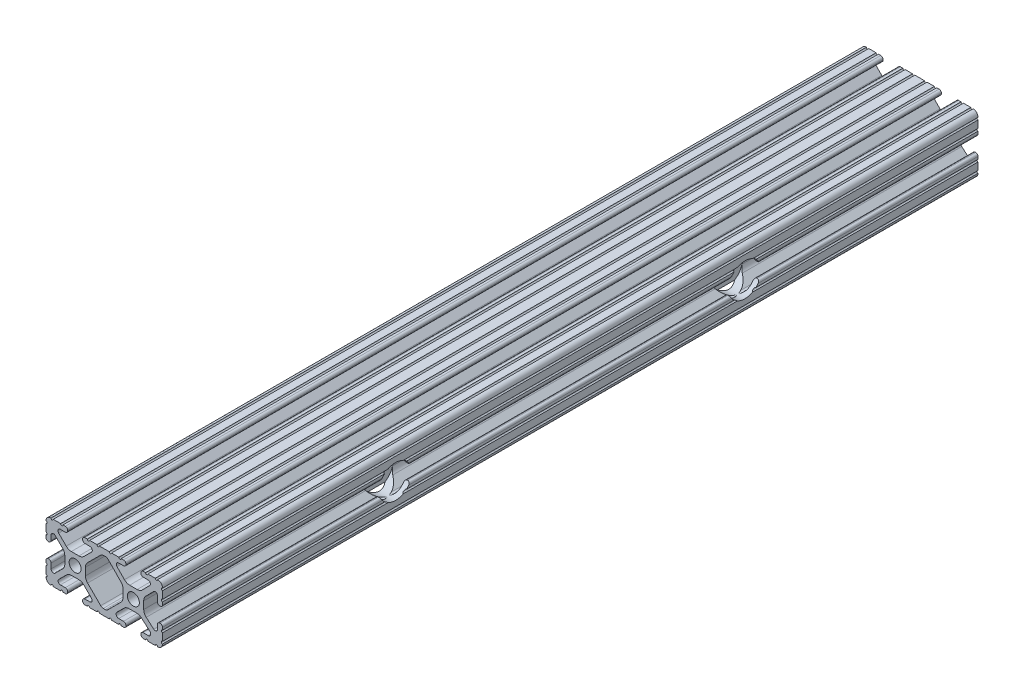
SolidWorks part; units mm, degrees
ref_plane "Front Plane" through (0, 0, 0) normal (0, 0, 1) x (1, 0, 0)
ref_plane "Top Plane" through (0, 0, 0) normal (0, 1, 0) x (1, 0, 0)
ref_plane "Right Plane" through (0, 0, 0) normal (1, 0, 0) x (0, 0, -1)
sketch "Sketch1" plane through (0, 0, 0) normal (0, 0, 1) x (1, 0, 0)
  line L0 (-7.2595, -3.8694) -> (-1.5457, -9.5728)
  line L1 (-8.1915, 1.6223) -> (-8.1915, -1.6223)
  line L2 (-1.504, 9.5765) -> (-7.252, 3.8768)
  line L3 (0.5515, 10.033) -> (-0.3952, 10.033)
  line L4 (7.2829, 3.8459) -> (1.6756, 9.5611)
  line L5 (8.1915, -1.6223) -> (8.1915, 1.6223)
  line L6 (1.5457, -9.5728) -> (7.2595, -3.8694)
  line L7 (-0.4332, -10.033) -> (0.4332, -10.033)
  line L8 (18.0171, 12.7) -> (16.9875, 12.7)
  line L9 (15.9385, 11.651) -> (15.9385, 11.5392)
  line L10 (16.9875, 10.4902) -> (19.1164, 10.4902)
  line L11 (19.8441, 8.7652) -> (16.619, 5.4551)
  line L12 (14.3449, 4.4958) -> (11.0833, 4.4958)
  line L13 (8.817, 5.4472) -> (5.5642, 8.7627)
  line L14 (6.2894, 10.4902) -> (8.4125, 10.4902)
  line L15 (9.4615, 11.5392) -> (9.4615, 11.651)
  line L16 (8.4125, 12.7) -> (7.3829, 12.7)
  line L17 (6.3669, 12.7) -> (3.1496, 12.7)
  line L18 (2.1336, 12.7) -> (-2.1336, 12.7)
  line L19 (-3.1496, 12.7) -> (-6.3669, 12.7)
  line L20 (-7.3829, 12.7) -> (-8.4125, 12.7)
  line L21 (-9.4615, 11.651) -> (-9.4615, 11.5392)
  line L22 (-8.4125, 10.4902) -> (-6.2836, 10.4902)
  line L23 (-5.5326, 8.6661) -> (-8.81, 5.4163)
  line L24 (-11.0455, 4.4958) -> (-14.3545, 4.4958)
  line L25 (-16.59, 5.4163) -> (-19.8674, 8.6661)
  line L26 (-19.1164, 10.4902) -> (-16.9875, 10.4902)
  line L27 (-15.9385, 11.5392) -> (-15.9385, 11.651)
  line L28 (-16.9875, 12.7) -> (-18.0171, 12.7)
  line L29 (-19.0331, 12.7) -> (-22.2504, 12.7)
  line L30 (-25.4, 9.5504) -> (-25.4, 6.3331)
  line L31 (-25.4, 5.3171) -> (-25.4, 4.2375)
  line L32 (-24.401, 3.2385) -> (-24.2392, 3.2385)
  line L33 (-23.1902, 4.2875) -> (-23.1902, 6.3347)
  line L34 (-21.434, 7.0665) -> (-18.148, 3.8082)
  line L35 (-17.2085, 1.5536) -> (-17.2085, -1.6952)
  line L36 (-18.1405, -3.9423) -> (-21.4316, -7.2274)
  line L37 (-23.1902, -6.498) -> (-23.1902, -4.2875)
  line L38 (-24.2392, -3.2385) -> (-24.351, -3.2385)
  line L39 (-25.4, -4.2875) -> (-25.4, -5.3171)
  line L40 (-25.4, -6.3331) -> (-25.4, -9.5504)
  line L41 (-22.2504, -12.7) -> (-19.0331, -12.7)
  line L42 (-18.0171, -12.7) -> (-16.9875, -12.7)
  line L43 (-15.9384, -11.651) -> (-15.9384, -11.5392)
  line L44 (-16.9875, -10.4902) -> (-19.1164, -10.4902)
  line L45 (-19.8341, -8.7551) -> (-16.4966, -5.4237)
  line L46 (-14.2536, -4.4958) -> (-11.1464, -4.4958)
  line L47 (-8.9034, -5.4237) -> (-5.5659, -8.7551)
  line L48 (-6.2836, -10.4902) -> (-8.4125, -10.4902)
  line L49 (-9.4616, -11.5392) -> (-9.4616, -11.651)
  line L50 (-8.4125, -12.7) -> (-7.3829, -12.7)
  line L51 (-6.3669, -12.7) -> (-3.1496, -12.7)
  line L52 (-2.1336, -12.7) -> (2.1336, -12.7)
  line L53 (3.1496, -12.7) -> (6.3669, -12.7)
  line L54 (7.3829, -12.7) -> (8.4125, -12.7)
  line L55 (9.4616, -11.651) -> (9.4616, -11.5392)
  line L56 (8.4125, -10.4902) -> (6.2894, -10.4902)
  line L57 (5.4807, -8.5353) -> (8.5979, -5.4237)
  line L58 (10.8409, -4.4958) -> (14.1026, -4.4958)
  line L59 (16.1879, -5.2766) -> (19.8682, -8.4822)
  line L60 (19.1164, -10.4902) -> (16.9875, -10.4902)
  line L61 (15.9384, -11.5392) -> (15.9384, -11.651)
  line L62 (16.9875, -12.7) -> (18.0171, -12.7)
  line L63 (19.0331, -12.7) -> (22.2504, -12.7)
  line L64 (25.4, -9.5504) -> (25.4, -6.3331)
  line L65 (25.4, -5.3171) -> (25.4, -4.2375)
  line L66 (24.401, -3.2385) -> (24.1892, -3.2385)
  line L67 (23.1902, -4.2375) -> (23.1902, -6.1559)
  line L68 (21.584, -6.8869) -> (18.2982, -4.025)
  line L69 (17.2085, -1.6308) -> (17.2085, 1.6308)
  line L70 (18.1094, 3.8465) -> (21.5263, 7.3534)
  line L71 (23.1902, 6.6769) -> (23.1902, 4.2375)
  line L72 (24.1892, 3.2385) -> (24.401, 3.2385)
  line L73 (25.4, 4.2375) -> (25.4, 5.3171)
  line L74 (25.4, 6.3332) -> (25.4, 9.5504)
  line L75 (22.2504, 12.7) -> (19.0331, 12.7)
  circle A0 centre (-12.7, 0) radius 2.6035
  circle A1 centre (12.7, 0) radius 2.6035
  arc A2 (-1.5457, -9.5728) -> (-0.4332, -10.033) centre (-0.4332, -8.4582) ccw
  arc A3 (-8.1915, -1.6223) -> (-7.2595, -3.8694) centre (-5.0165, -1.6223) ccw
  arc A4 (-7.252, 3.8768) -> (-8.1915, 1.6223) centre (-5.0165, 1.6223) ccw
  arc A5 (-0.3952, 10.033) -> (-1.504, 9.5765) centre (-0.3952, 8.4582) ccw
  arc A6 (1.6756, 9.5611) -> (0.5515, 10.033) centre (0.5515, 8.4582) ccw
  arc A7 (8.1915, 1.6223) -> (7.2829, 3.8459) centre (5.0165, 1.6223) ccw
  arc A8 (7.2595, -3.8694) -> (8.1915, -1.6223) centre (5.0165, -1.6223) ccw
  arc A9 (0.4332, -10.033) -> (1.5457, -9.5728) centre (0.4332, -8.4582) ccw
  arc A10 (18.0171, 12.7) -> (19.0331, 12.7) centre (18.5251, 12.7) ccw
  arc A11 (16.9875, 12.7) -> (15.9385, 11.651) centre (16.9875, 11.651) ccw
  arc A12 (15.9385, 11.5392) -> (16.9875, 10.4902) centre (16.9875, 11.5392) ccw
  arc A13 (19.8441, 8.7652) -> (19.1164, 10.4902) centre (19.1164, 9.4742) ccw
  arc A14 (14.3449, 4.4958) -> (16.619, 5.4551) centre (14.3449, 7.6708) ccw
  arc A15 (8.817, 5.4472) -> (11.0833, 4.4958) centre (11.0833, 7.6708) ccw
  arc A16 (6.2894, 10.4902) -> (5.5642, 8.7627) centre (6.2894, 9.4742) ccw
  arc A17 (8.4125, 10.4902) -> (9.4615, 11.5392) centre (8.4125, 11.5392) ccw
  arc A18 (9.4615, 11.651) -> (8.4125, 12.7) centre (8.4125, 11.651) ccw
  arc A19 (6.3669, 12.7) -> (7.3829, 12.7) centre (6.8749, 12.7) ccw
  arc A20 (2.1336, 12.7) -> (3.1496, 12.7) centre (2.6416, 12.7) ccw
  arc A21 (-3.1496, 12.7) -> (-2.1336, 12.7) centre (-2.6416, 12.7) ccw
  arc A22 (-7.3829, 12.7) -> (-6.3669, 12.7) centre (-6.8749, 12.7) ccw
  arc A23 (-8.4125, 12.7) -> (-9.4615, 11.651) centre (-8.4125, 11.651) ccw
  arc A24 (-9.4615, 11.5392) -> (-8.4125, 10.4902) centre (-8.4125, 11.5392) ccw
  arc A25 (-5.5326, 8.6661) -> (-6.2836, 10.4902) centre (-6.2836, 9.4235) ccw
  arc A26 (-11.0455, 4.4958) -> (-8.81, 5.4163) centre (-11.0455, 7.6708) ccw
  arc A27 (-16.59, 5.4163) -> (-14.3545, 4.4958) centre (-14.3545, 7.6708) ccw
  arc A28 (-19.1164, 10.4902) -> (-19.8674, 8.6661) centre (-19.1164, 9.4235) ccw
  arc A29 (-16.9875, 10.4902) -> (-15.9385, 11.5392) centre (-16.9875, 11.5392) ccw
  arc A30 (-15.9385, 11.651) -> (-16.9875, 12.7) centre (-16.9875, 11.651) ccw
  arc A31 (-19.0331, 12.7) -> (-18.0171, 12.7) centre (-18.5251, 12.7) ccw
  arc A32 (-23.2664, 12.6998) -> (-22.2504, 12.7) centre (-22.7584, 12.7) ccw
  arc A33 (-23.2664, 12.6998) -> (-25.3998, 10.5664) centre (-23.2918, 10.5918) ccw
  arc A34 (-25.4, 9.5504) -> (-25.3998, 10.5664) centre (-25.4, 10.0584) ccw
  arc A35 (-25.4, 5.3171) -> (-25.4, 6.3331) centre (-25.4, 5.8251) ccw
  arc A36 (-25.4, 4.2375) -> (-24.401, 3.2385) centre (-24.401, 4.2375) ccw
  arc A37 (-24.2392, 3.2385) -> (-23.1902, 4.2875) centre (-24.2392, 4.2875) ccw
  arc A38 (-21.434, 7.0665) -> (-23.1902, 6.3347) centre (-22.1596, 6.3347) ccw
  arc A39 (-17.2085, 1.5536) -> (-18.148, 3.8082) centre (-20.3835, 1.5536) ccw
  arc A40 (-18.1405, -3.9423) -> (-17.2085, -1.6952) centre (-20.3835, -1.6952) ccw
  arc A41 (-23.1902, -6.498) -> (-21.4316, -7.2274) centre (-22.1596, -6.498) ccw
  arc A42 (-23.1902, -4.2875) -> (-24.2392, -3.2385) centre (-24.2392, -4.2875) ccw
  arc A43 (-24.351, -3.2385) -> (-25.4, -4.2875) centre (-24.351, -4.2875) ccw
  arc A44 (-25.4, -6.3331) -> (-25.4, -5.3171) centre (-25.4, -5.8251) ccw
  arc A45 (-25.3998, -10.5664) -> (-25.4, -9.5504) centre (-25.4, -10.0584) ccw
  arc A46 (-25.3998, -10.5664) -> (-23.2664, -12.6998) centre (-23.2918, -10.5918) ccw
  arc A47 (-22.2504, -12.7) -> (-23.2664, -12.6998) centre (-22.7584, -12.7) ccw
  arc A48 (-18.0171, -12.7) -> (-19.0331, -12.7) centre (-18.5251, -12.7) ccw
  arc A49 (-16.9875, -12.7) -> (-15.9384, -11.651) centre (-16.9875, -11.651) ccw
  arc A50 (-15.9384, -11.5392) -> (-16.9875, -10.4902) centre (-16.9875, -11.5392) ccw
  arc A51 (-19.8341, -8.7551) -> (-19.1164, -10.4902) centre (-19.1164, -9.4742) ccw
  arc A52 (-14.2536, -4.4958) -> (-16.4966, -5.4237) centre (-14.2536, -7.6708) ccw
  arc A53 (-8.9034, -5.4237) -> (-11.1464, -4.4958) centre (-11.1464, -7.6708) ccw
  arc A54 (-6.2836, -10.4902) -> (-5.5659, -8.7551) centre (-6.2836, -9.4742) ccw
  arc A55 (-8.4125, -10.4902) -> (-9.4616, -11.5392) centre (-8.4125, -11.5392) ccw
  arc A56 (-9.4616, -11.651) -> (-8.4125, -12.7) centre (-8.4125, -11.651) ccw
  arc A57 (-6.3669, -12.7) -> (-7.3829, -12.7) centre (-6.8749, -12.7) ccw
  arc A58 (-2.1336, -12.7) -> (-3.1496, -12.7) centre (-2.6416, -12.7) ccw
  arc A59 (3.1496, -12.7) -> (2.1336, -12.7) centre (2.6416, -12.7) ccw
  arc A60 (7.3829, -12.7) -> (6.3669, -12.7) centre (6.8749, -12.7) ccw
  arc A61 (8.4125, -12.7) -> (9.4616, -11.651) centre (8.4125, -11.651) ccw
  arc A62 (9.4616, -11.5392) -> (8.4125, -10.4902) centre (8.4125, -11.5392) ccw
  arc A63 (5.4807, -8.5353) -> (6.2894, -10.4902) centre (6.2894, -9.3455) ccw
  arc A64 (10.8409, -4.4958) -> (8.5979, -5.4237) centre (10.8409, -7.6708) ccw
  arc A65 (16.1879, -5.2766) -> (14.1026, -4.4958) centre (14.1026, -7.6708) ccw
  arc A66 (19.1164, -10.4902) -> (19.8682, -8.4822) centre (19.1164, -9.3455) ccw
  arc A67 (16.9875, -10.4902) -> (15.9384, -11.5392) centre (16.9875, -11.5392) ccw
  arc A68 (15.9384, -11.651) -> (16.9875, -12.7) centre (16.9875, -11.651) ccw
  arc A69 (19.0331, -12.7) -> (18.0171, -12.7) centre (18.5251, -12.7) ccw
  arc A70 (23.2664, -12.6998) -> (22.2504, -12.7) centre (22.7584, -12.7) ccw
  arc A71 (23.2664, -12.6998) -> (25.3998, -10.5664) centre (23.2918, -10.5918) ccw
  arc A72 (25.4, -9.5504) -> (25.3998, -10.5664) centre (25.4, -10.0584) ccw
  arc A73 (25.4, -5.3171) -> (25.4, -6.3331) centre (25.4, -5.8251) ccw
  arc A74 (25.4, -4.2375) -> (24.401, -3.2385) centre (24.401, -4.2375) ccw
  arc A75 (24.1892, -3.2385) -> (23.1902, -4.2375) centre (24.1892, -4.2375) ccw
  arc A76 (21.584, -6.8869) -> (23.1902, -6.1559) centre (22.2207, -6.1559) ccw
  arc A77 (17.2085, -1.6308) -> (18.2982, -4.025) centre (20.3835, -1.6308) ccw
  arc A78 (18.1094, 3.8465) -> (17.2085, 1.6308) centre (20.3835, 1.6308) ccw
  arc A79 (23.1902, 6.6769) -> (21.5263, 7.3534) centre (22.2207, 6.6769) ccw
  arc A80 (23.1902, 4.2375) -> (24.1892, 3.2385) centre (24.1892, 4.2375) ccw
  arc A81 (24.401, 3.2385) -> (25.4, 4.2375) centre (24.401, 4.2375) ccw
  arc A82 (25.4, 6.3332) -> (25.4, 5.3171) centre (25.4, 5.8251) ccw
  arc A83 (25.3998, 10.5664) -> (25.4, 9.5504) centre (25.4, 10.0584) ccw
  arc A84 (25.3998, 10.5664) -> (23.2664, 12.6998) centre (23.2918, 10.5918) ccw
  arc A85 (22.2504, 12.7) -> (23.2664, 12.6998) centre (22.7584, 12.7) ccw
  point P248 (0, 10.033)
extrude "Boss-Extrude1" add sketch "Sketch1" along normal mid plane 355.6
hole_wizard "CBORE for 1/4 Binding Head Machine Screw1" positions "Sketch3" profile "Sketch5" counterbore size "1/4" standard "ANSI Inch" end condition through all
sketch "Sketch3" plane through (25.4, 0, 0) normal (1, 0, 0) x (0, 0, -1)
  line L0 (-76.2, 0) -> (76.2, 0) construction
  point P0 (-76.2, 0)
  point P2 (76.2, 0)
  point P9 (0, 0)
  dimension "D1" = 152.4
sketch "Sketch5" plane through (25.4, 0, 76.2) normal (0, 1, 0) x (0, 0, -1)
  line L0 (0, 0) -> (0, 50.8)
  line L1 (0, 50.8) -> (3.3782, 50.8)
  line L3 (3.3782, 50.8) -> (3.3782, 8.255)
  line L4 (3.3782, 8.255) -> (7.1437, 8.255)
  line L5 (7.1437, 8.255) -> (7.1437, 0)
  line L7 (7.1437, 0) -> (0, 0)
  line L11 (0, -6.35) -> (0, 107.95) construction
  dimension "Thru Hole Dia." = 6.7564
  dimension "Thru Hole Depth" = 50.8
  dimension "C'Bore Dia." = 14.2875
  dimension "C'Bore Depth" = 8.255
